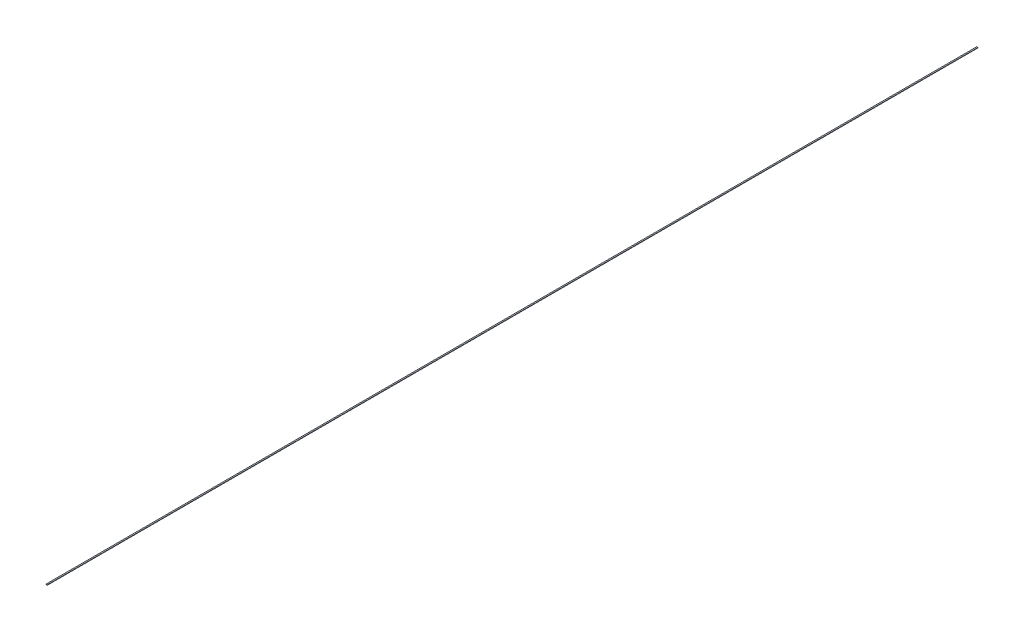
SolidWorks part; units mm, degrees
ref_plane "Front Plane" through (0, 0, 0) normal (0, 0, 1) x (1, 0, 0)
ref_plane "Top Plane" through (0, 0, 0) normal (0, 1, 0) x (1, 0, 0)
ref_plane "Right Plane" through (0, 0, 0) normal (1, 0, 0) x (0, 0, -1)
sketch "Sketch1" plane through (0, 0, 0) normal (0, 0, 1) x (1, 0, 0)
  line L1 (0, 0) -> (0.6, 0)
  line L2 (0, 0) -> (0, 0.2)
  line L3 (0, 0.2) -> (0.6, 0.2)
  line L4 (0.6, 0) -> (0.6, 0.2)
  dimension "D1" = 0.6
  dimension "D2" = 0.2
extrude "Boss-Extrude1" add sketch "Sketch1" along normal blind 450
